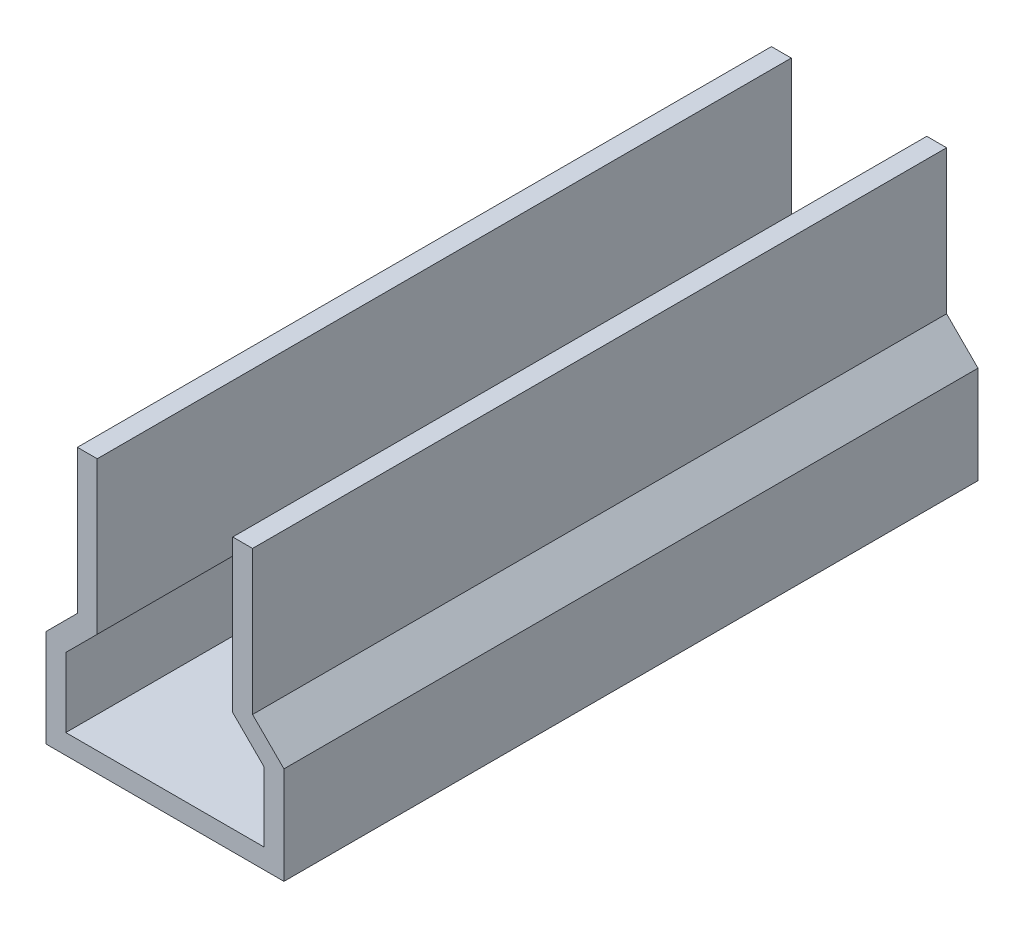
SolidWorks part; units mm, degrees
ref_plane "Front Plane" through (0, 0, 0) normal (0, 0, 1) x (1, 0, 0)
ref_plane "Top Plane" through (0, 0, 0) normal (0, 1, 0) x (1, 0, 0)
ref_plane "Right Plane" through (0, 0, 0) normal (1, 0, 0) x (0, 0, -1)
sketch "Sketch1" plane through (0, 0, 0) normal (0, 0, 1) x (1, 0, 0)
  line L0 (15, 0) -> (-15, 0)
  line L1 (-15, 0) -> (-15, 10.5)
  line L2 (0, 39.3262) -> (0, -43.6107) construction
  line L3 (15, 0) -> (15, 10.5)
  line L4 (10.25, 35.25) -> (-10.25, 35.25)
  line L5 (-10.25, 35.25) -> (-10.25, 15.25)
  line L6 (10.25, 35.25) -> (10.25, 15.25)
  line L7 (-15, 10.5) -> (-10.25, 15.25)
  line L8 (15, 10.5) -> (10.25, 15.25)
  line L9 (18, 11.7426) -> (13.25, 16.4926)
  line L10 (13.25, 38.25) -> (13.25, 16.4926)
  line L11 (13.25, 38.25) -> (-13.25, 38.25)
  line L12 (-13.25, 38.25) -> (-13.25, 16.4926)
  line L13 (-18, 11.7426) -> (-13.25, 16.4926)
  line L14 (-18, -3) -> (-18, 11.7426)
  line L15 (18, -3) -> (-18, -3)
  line L16 (18, -3) -> (18, 11.7426)
  point P4 (0, 0)
  point P12 (0, 35.25)
  dimension "D1" = 30
  dimension "D2" = 10.5
  dimension "D3" = 20.5
  dimension "D4" = 20
  dimension "D5" = 135
  dimension "D6" = 3
extrude "Boss-Extrude1" add sketch "Sketch1" along normal blind 105
sketch "Sketch2" plane through (0, 0, 105) normal (0, 0, 1) x (1, 0, 0)
  line L0 (13.25, 38.25) -> (-13.25, 38.25) construction
  line L1 (-10.25, 35.25) -> (10.25, 35.25)
  line L2 (-10.25, 35.25) -> (-10.25, 38.25)
  line L3 (-10.25, 38.25) -> (10.25, 38.25)
  line L4 (10.25, 35.25) -> (10.25, 38.25)
extrude "Cut-Extrude1" cut sketch "Sketch2" against normal through all both and the other way through all
